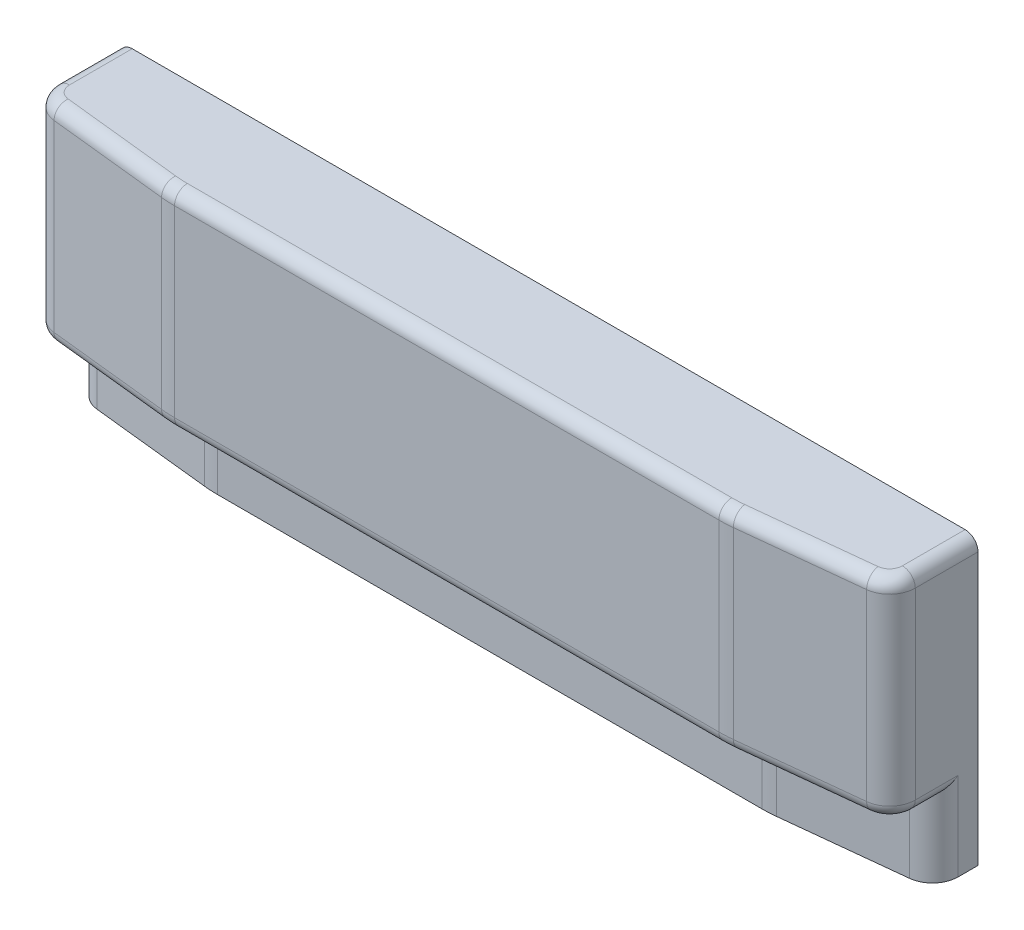
SolidWorks part; units mm, degrees
other "Camera1"
ref_plane "Front Plane" through (0, 0, 0) normal (0, 0, 1) x (1, 0, 0)
ref_plane "Top Plane" through (0, 0, 0) normal (0, 1, 0) x (1, 0, 0)
ref_plane "Right Plane" through (0, 0, 0) normal (1, 0, 0) x (0, 0, -1)
sketch "Sketch7" plane through (0, 0, 0) normal (0, 1, 0) x (1, 0, 0)
  line L0 (0, 0) -> (508, 0)
  line L1 (508, 0) -> (508, -50.8)
  line L2 (508, -50.8) -> (419.1, -60.325)
  line L3 (419.1, -60.325) -> (88.9, -60.325)
  line L4 (88.9, -60.325) -> (0, -50.8)
  line L5 (0, -50.8) -> (0, 0)
  line L6 (254, 0) -> (254, -60.325) construction
  point P9 (254, -60.325)
  dimension "D1" = 508
  dimension "D2" = 50.8
  dimension "D3" = 88.9
  dimension "D4" = 88.9
  dimension "D5" = 60.325
extrude "Boss-Extrude1" add sketch "Sketch7" along normal blind 168.275
ref_plane "Wall Plane" through (0, 0, 0) normal (0, 0, 1) x (1, 0, 0)
ref_plane "Floor Plane" through (0, 0, 0) normal (0, 1, 0) x (1, 0, 0)
sketch "Sketch10" plane through (0, 0, 0) normal (0, -1, 0) x (1, 0, 0)
  line L0 (0, 50.8) -> (0, 25.4)
  line L1 (0, 0) -> (0, 50.8) construction
  line L2 (0, 25.4) -> (88.9, 34.925)
  line L3 (88.9, 34.925) -> (419.1, 34.925)
  line L4 (419.1, 34.925) -> (508, 25.4)
  line L5 (508, 50.8) -> (508, 0) construction
  line L6 (508, 25.4) -> (508, 50.8)
  line L7 (508, 50.8) -> (419.1, 60.325)
  line L8 (419.1, 60.325) -> (88.9, 60.325)
  line L9 (88.9, 60.325) -> (0, 50.8)
  dimension "D1" = 25.4
extrude "Cut-Extrude1" cut sketch "Sketch10" against normal blind 44.45
fillet "Fillet1" radius 15.24 4 edges at (508, 22.225, 25.4) (508, 106.3625, 50.8) (0, 22.225, 25.4) (0, 106.3625, 50.8)
fillet "Fillet2" radius 76.2 4 edges at (419.1, 22.225, 34.925) (419.1, 106.3625, 60.325) (88.9, 22.225, 34.925) (88.9, 106.3625, 60.325)
fillet "Fillet3" radius 7.62 9 edges at (0, 168.275, 18.5528) (3.9042, 168.275, 47.2918) (49.2346, 168.275, 56.0751) (88.9058, 168.275, 60.2165) (508, 168.275, 18.5528) (504.0958, 168.275, 47.2918) (458.7654, 168.275, 56.0751) (419.0942, 168.275, 60.2165) (254, 168.275, 60.325)
fillet "Fillet4" radius 7.62 9 edges at (508, 44.45, 24.4056) (504.0958, 44.45, 47.2918) (458.7654, 44.45, 56.0751) (419.0942, 44.45, 60.2165) (0, 44.45, 24.4056) (3.9042, 44.45, 47.2918) (49.2346, 44.45, 56.0751) (88.9058, 44.45, 60.2165) (254, 44.45, 60.325)
ref_plane "Mid-Plane" through (254, 0, 0) normal (1, 0, 0) x (0, 0, -1)
